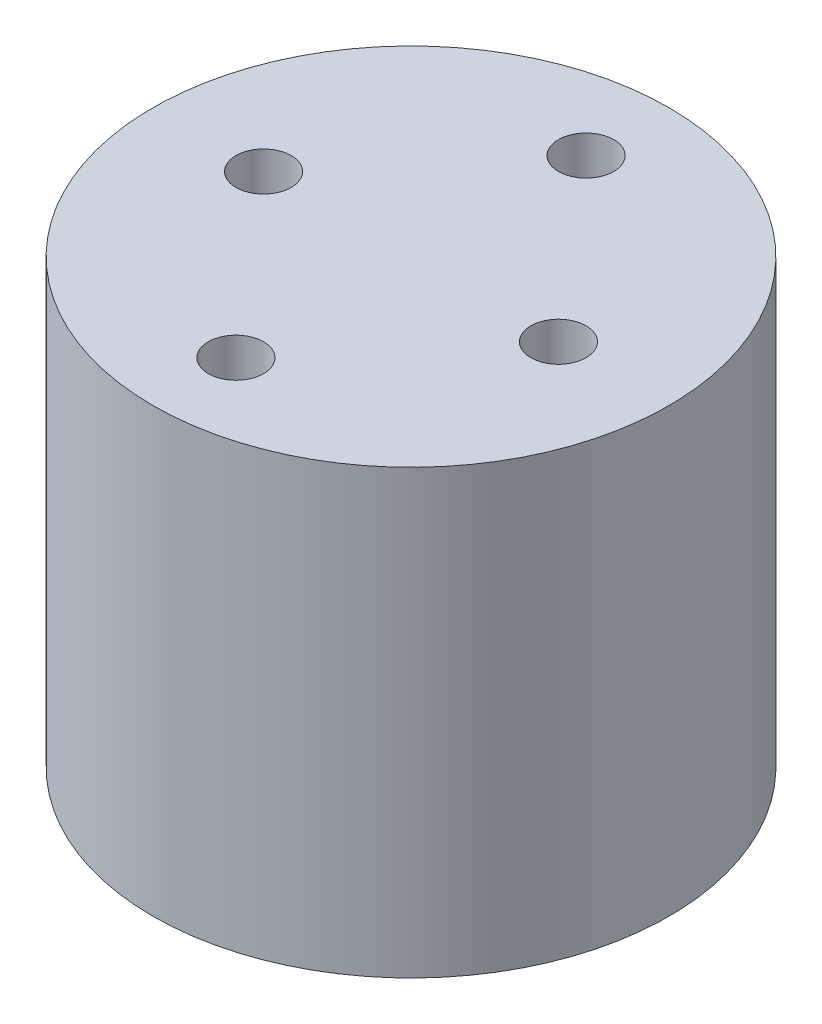
SolidWorks part; units mm, degrees
ref_plane "Front Plane" through (0, 0, 0) normal (0, 0, 1) x (1, 0, 0)
ref_plane "Top Plane" through (0, 0, 0) normal (0, 1, 0) x (1, 0, 0)
ref_plane "Right Plane" through (0, 0, 0) normal (1, 0, 0) x (0, 0, -1)
sketch "Sketch1" plane through (0, 0, 0) normal (0, 1, 0) x (1, 0, 0)
  circle A0 centre (0, 0) radius 14
  dimension "D1" = 28
extrude "Boss-Extrude1" add sketch "Sketch1" along normal blind 24
sketch "Sketch2" plane through (0, 24, 0) normal (0, 1, 0) x (1, 0, 0)
  line L0 (-13.2, 0) -> (13.2, 0) construction
  line L1 (0, -13.2) -> (0, 13.2) construction
  circle A0 centre (-8, 0) radius 1.5
  circle A1 centre (0, 9.5) radius 1.5
  circle A2 centre (0, -9.5) radius 1.5
  circle A3 centre (8, 0) radius 1.5
  dimension "D1" = 3
  dimension "D2" = 8
  dimension "D3" = 9.5
extrude "Cut-Extrude1" cut sketch "Sketch2" against normal blind 3 contours A3 | A1 | A0 | A2
sketch "Sketch3" plane through (0, 0, 0) normal (0, -1, 0) x (1, 0, 0)
  circle A0 centre (0, 0) radius 4
  dimension "D1" = 8
extrude "Boss-Extrude2" add sketch "Sketch3" along normal blind 2
